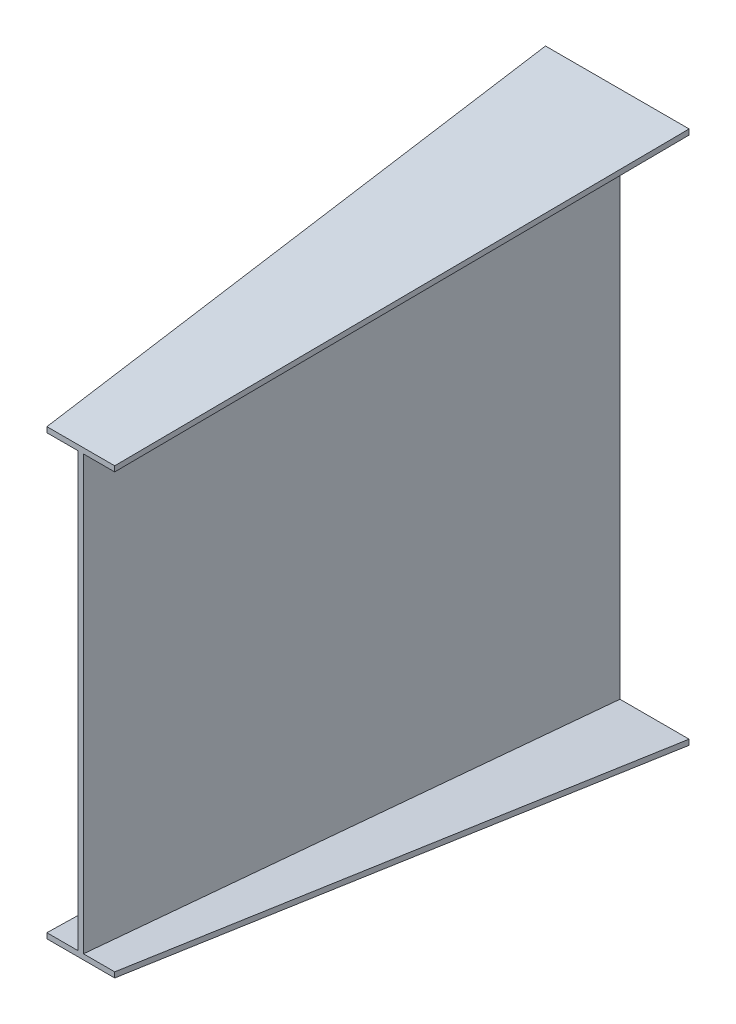
SolidWorks part; units mm, degrees
ref_plane "Front Plane" through (0, 0, 0) normal (0, 0, 1) x (1, 0, 0)
ref_plane "Top Plane" through (0, 0, 0) normal (0, 1, 0) x (1, 0, 0)
ref_plane "Right Plane" through (0, 0, 0) normal (1, 0, 0) x (0, 0, -1)
sketch "Sketch1" plane through (0, 0, 0) normal (0, 0, 1) x (1, 0, 0)
  line L0 (-129.5, 0) -> (0, 0)
  line L2 (0, 0) -> (0, 980)
  line L4 (10, 0) -> (10, 980)
  line L5 (-129.5, 980) -> (0, 980)
  line L6 (-129.5, 980) -> (-129.5, 990)
  line L7 (-129.5, 990) -> (139.5, 990)
  line L8 (139.5, 980) -> (139.5, 990)
  line L9 (139.5, -10) -> (139.5, 0)
  line L10 (-129.5, -10) -> (-129.5, 0)
  line L11 (-129.5, -10) -> (139.5, -10)
  line L12 (10, 0) -> (139.5, 0)
  line L13 (10, 980) -> (139.5, 980)
  dimension "D1" = 10
  dimension "D2" = 980
  dimension "D3" = 10
  dimension "D4" = 269
  dimension "D5" = 129.5
  dimension "D6" = 269
  dimension "D7" = 129.5
ref_plane "Plane1" through (0, 0, 1000) normal (0, 0, 1) x (1, 0, 0)
sketch "Sketch3" plane through (0, 0, 1000) normal (0, 0, 1) x (1, 0, 0)
  line L1 (-63.5, 895.5) -> (-5, 895.5)
  line L2 (-63.5, 74.5) -> (63.5, 74.5)
  line L3 (-63.5, 74.5) -> (-63.5, 84.5)
  line L4 (-63.5, 84.5) -> (-5, 84.5)
  line L5 (63.5, 74.5) -> (63.5, 84.5)
  line L7 (-5, 84.5) -> (-5, 895.5)
  line L9 (5, 84.5) -> (5, 895.5)
  line L10 (-63.5, 895.5) -> (-63.5, 905.5)
  line L11 (63.5, 895.5) -> (63.5, 905.5)
  line L12 (-63.5, 905.5) -> (63.5, 905.5)
  line L13 (5, 895.5) -> (63.5, 895.5)
  line L14 (5, 84.5) -> (63.5, 84.5)
  dimension "D2" = 10
  dimension "D3" = 127
  dimension "D4" = 58.5
  dimension "D5" = 10
  dimension "D7" = 811
  dimension "D8" = 127
  dimension "D9" = 10
  dimension "D10" = 58.5
loft "Loft2" add profiles "Sketch1", "Sketch3"
